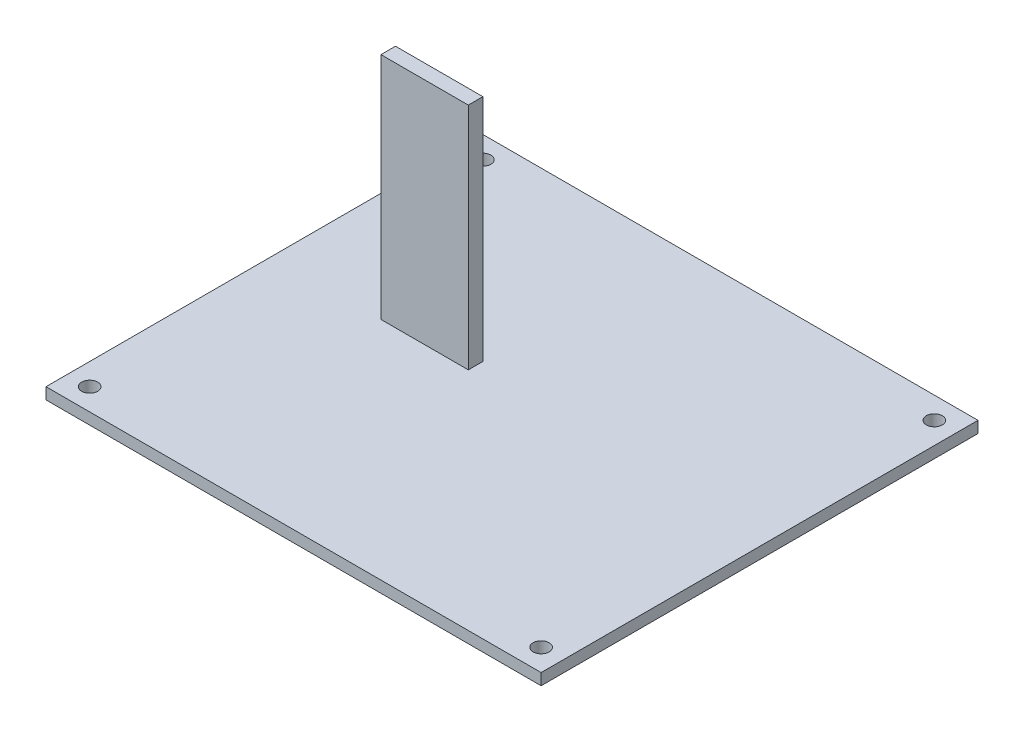
SolidWorks part; units mm, degrees
ref_plane "Front Plane" through (0, 0, 0) normal (0, 0, 1) x (1, 0, 0)
ref_plane "Top Plane" through (0, 0, 0) normal (0, 1, 0) x (1, 0, 0)
ref_plane "Right Plane" through (0, 0, 0) normal (1, 0, 0) x (0, 0, -1)
sketch "Sketch1" plane through (0, 0, 0) normal (0, 1, 0) x (1, 0, 0)
  line L1 (-43.18, -38.1) -> (43.18, -38.1)
  line L2 (-43.18, -38.1) -> (-43.18, 38.1)
  line L3 (-43.18, 38.1) -> (43.18, 38.1)
  line L4 (43.18, -38.1) -> (43.18, 38.1)
  line L5 (-43.18, -38.1) -> (43.18, 38.1) construction
  line L6 (-43.18, 38.1) -> (43.18, -38.1) construction
  circle A0 centre (-39.37, 34.29) radius 1.397
  circle A1 centre (39.37, -34.29) radius 1.397
  circle A2 centre (-39.37, -34.29) radius 1.397
  circle A3 centre (39.37, 34.29) radius 1.397
  point P0 (0, 0)
  dimension "D5" = 2.794
  dimension "D6" = 3.81
  dimension "D1" = 86.36
  dimension "D2" = 76.2
  dimension "D3" = 3.81
  dimension "D4" = 3.81
  dimension "D7" = 3.81
extrude "Boss-Extrude1" add sketch "Sketch1" along normal blind 2
sketch "Sketch2" plane through (0, 2, 0) normal (0, 1, 0) x (1, 0, 0)
  line L2 (-43.18, 38.1) -> (-43.18, -38.1) construction
  line L3 (-24.13, 3.81) -> (-8.89, 3.81)
  line L4 (-24.13, 3.81) -> (-24.13, 1.27)
  line L5 (-24.13, 1.27) -> (-8.89, 1.27)
  line L6 (-8.89, 3.81) -> (-8.89, 1.27)
  line L7 (-24.13, 3.81) -> (-8.89, 1.27) construction
  line L8 (-24.13, 1.27) -> (-8.89, 3.81) construction
  line L9 (43.18, 38.1) -> (-43.18, 38.1) construction
  point P4 (-16.51, 2.54)
  dimension "D1" = 15.24
  dimension "D2" = 2.54
  dimension "D3" = 19.05
  dimension "D4" = 34.29
extrude "Boss-Extrude2" add sketch "Sketch2" along normal blind 40
